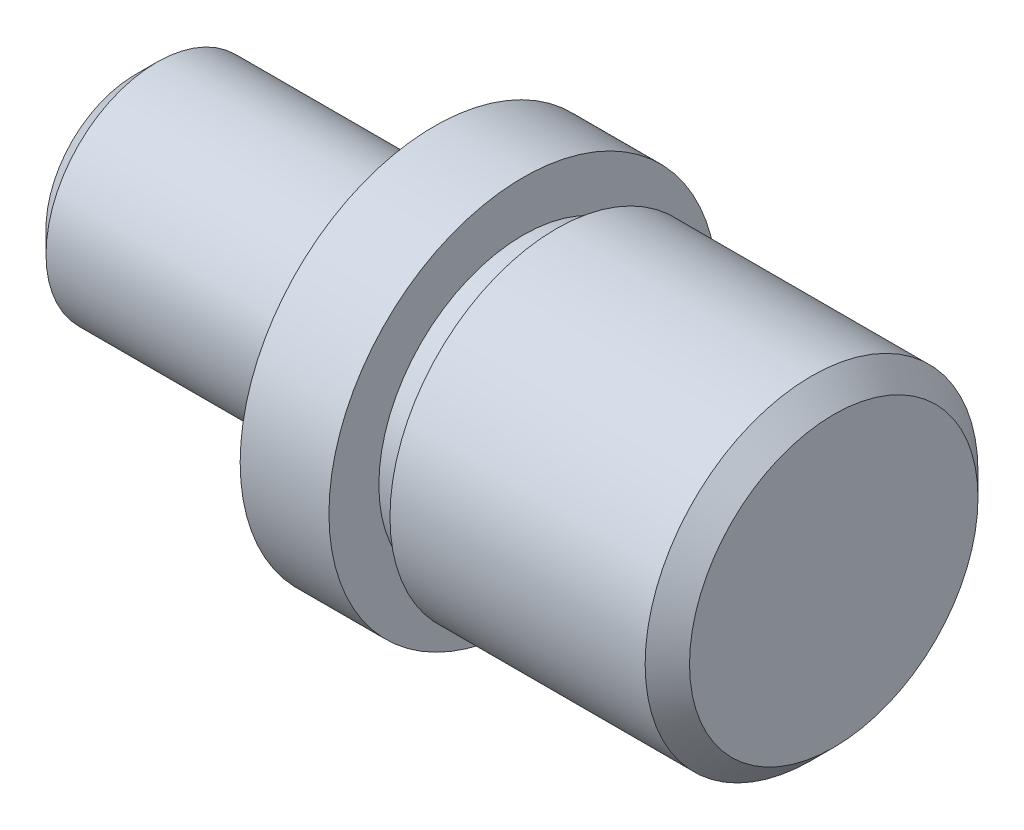
SolidWorks part; units mm, degrees
ref_plane "前视基准面" through (0, 0, 0) normal (0, 0, 1) x (1, 0, 0)
ref_plane "上视基准面" through (0, 0, 0) normal (0, 1, 0) x (1, 0, 0)
ref_plane "右视基准面" through (0, 0, 0) normal (1, 0, 0) x (0, 0, -1)
sketch "草图1" plane through (0, 0, 0) normal (0, 0, 1) x (1, 0, 0)
  line L1 (-82.8443, 0) -> (49917.1557, 0) construction
  line L4 (0, 0) -> (0, 10)
  line L5 (0, -55) -> (0, 55) construction
  line L6 (0, 10) -> (25, 10)
  line L7 (25, 10) -> (25, 8)
  line L8 (25, 8) -> (27, 8)
  line L9 (27, 8) -> (27, 17.5)
  line L10 (27, 17.5) -> (35, 17.5)
  line L11 (35, 17.5) -> (35, 13)
  line L12 (35, 13) -> (38, 13)
  line L13 (38, 13) -> (38, 15)
  line L14 (38, 15) -> (63, 15)
  line L15 (63, 15) -> (63, 0)
  line L16 (63, 0) -> (0, 0)
  dimension "D1" = 20
  dimension "D2" = 25
  dimension "D3" = 2
  dimension "D4" = 2
  dimension "D5" = 8
  dimension "D6" = 3
  dimension "D7" = 25
  dimension "D8" = 35
  dimension "D9" = 30
  dimension "D10" = 2
revolve "旋转1" add sketch "草图1" angle 360 about L1
chamfer "倒角1" distance 2 angle 45 2 edges at (63, 0, 15) (0, 0, 10)
